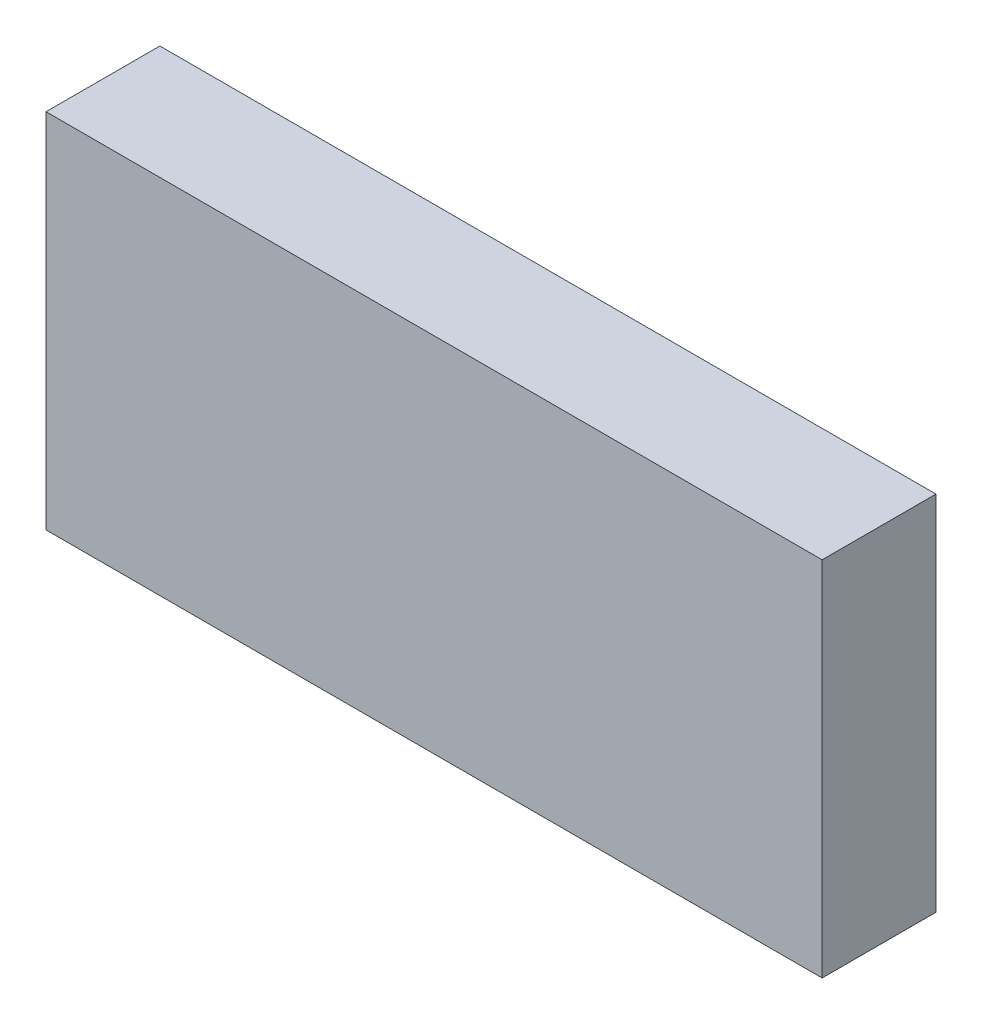
SolidWorks part; units mm, degrees
ref_plane "Plan de face" through (0, 0, 0) normal (0, 0, 1) x (1, 0, 0)
ref_plane "Plan de dessus" through (0, 0, 0) normal (0, 1, 0) x (1, 0, 0)
ref_plane "Plan de droite" through (0, 0, 0) normal (1, 0, 0) x (0, 0, -1)
sketch "Esquisse1" plane through (0, 0, 0) normal (0, 0, 1) x (1, 0, 0)
  line L1 (-75, 35) -> (75, 35)
  line L2 (-75, 35) -> (-75, -35)
  line L3 (-75, -35) -> (75, -35)
  line L4 (75, 35) -> (75, -35)
  line L5 (-75, 35) -> (75, -35) construction
  line L6 (-75, -35) -> (75, 35) construction
  point P0 (0, 0)
  dimension "D1" = 150
  dimension "D2" = 70
extrude "Boss.-Extru.1" add sketch "Esquisse1" along normal blind 22
